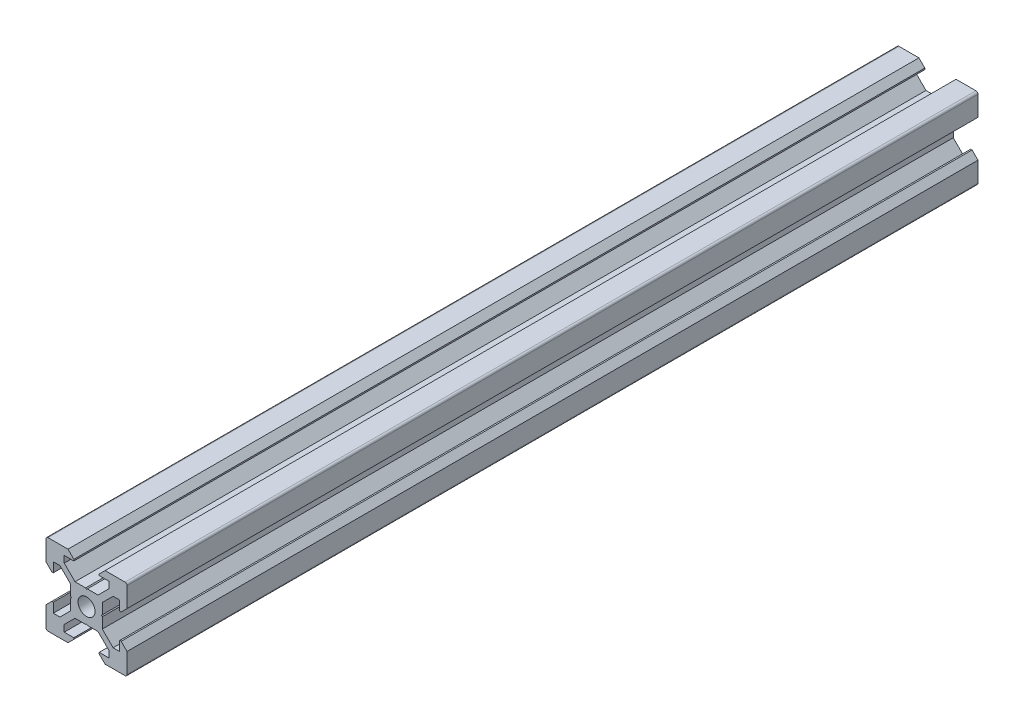
SolidWorks part; units mm, degrees
material "6061-T6 (SS)"
ref_plane "Front Plane" through (0, 0, 0) normal (0, 0, 1) x (1, 0, 0)
ref_plane "Top Plane" through (0, 0, 0) normal (0, 1, 0) x (1, 0, 0)
ref_plane "Right Plane" through (0, 0, 0) normal (1, 0, 0) x (0, 0, -1)
sketch "Sketch1" plane through (0, 0, 0) normal (0, 0, 1) x (1, 0, 0)
  line L1 (9.5, -10) -> (-9.5, -10)
  line L2 (10, -9.5) -> (10, 9.5)
  line L3 (9.5, 10) -> (-9.5, 10)
  line L4 (-10, -9.5) -> (-10, 9.5)
  line L5 (10, -10) -> (-10, 10) construction
  line L6 (10, 10) -> (-10, -10) construction
  circle A0 centre (0, 0) radius 2.1
  arc A1 (-9.5, 10) -> (-10, 9.5) centre (-9.5, 9.5) ccw
  arc A2 (10, 9.5) -> (9.5, 10) centre (9.5, 9.5) ccw
  arc A3 (9.5, -10) -> (10, -9.5) centre (9.5, -9.5) ccw
  arc A4 (-9.5, -10) -> (-10, -9.5) centre (-9.5, -9.5) cw
  point P0 (0, 0)
  line B0 (0, 0) -> (0, 10) construction
  line B1 (0, 3.69) -> (-0.21, 3.9)
  line B2 (-0.21, 3.9) -> (-2.8393, 3.9)
  line B3 (-2.8393, 3.9) -> (-5.5, 6.5607)
  line B4 (-5.5, 6.5607) -> (-5.5, 8.2)
  line B5 (-5.5, 8.2) -> (-3.125, 8.2)
  line B6 (-3.125, 8.2) -> (-3.125, 8.545)
  line B7 (-3.125, 8.545) -> (-4.58, 10)
  line B8 (-4.58, 10) -> (4.58, 10)
  line B9 (0, 0) -> (-5.9132, 5.9132) construction
  line B10 (3.125, 8.545) -> (4.58, 10)
  line B11 (3.125, 8.2) -> (3.125, 8.545)
  line B12 (5.5, 8.2) -> (3.125, 8.2)
  line B13 (5.5, 6.5607) -> (5.5, 8.2)
  line B14 (2.8393, 3.9) -> (5.5, 6.5607)
  line B15 (0.21, 3.9) -> (2.8393, 3.9)
  line B16 (0, 3.69) -> (0.21, 3.9)
  line B17 (0, 0) -> (-10, 0) construction
  line B18 (-3.69, 0) -> (-3.9, -0.21)
  line B19 (-3.9, -0.21) -> (-3.9, -2.8393)
  line B20 (-3.9, -2.8393) -> (-6.5607, -5.5)
  line B21 (-6.5607, -5.5) -> (-8.2, -5.5)
  line B22 (-8.2, -5.5) -> (-8.2, -3.125)
  line B23 (-8.2, -3.125) -> (-8.545, -3.125)
  line B24 (-8.545, -3.125) -> (-10, -4.58)
  line B25 (-10, -4.58) -> (-10, 4.58)
  line B26 (0, 0) -> (-5.9132, -5.9132) construction
  line B27 (-8.545, 3.125) -> (-10, 4.58)
  line B28 (-8.2, 3.125) -> (-8.545, 3.125)
  line B29 (-8.2, 5.5) -> (-8.2, 3.125)
  line B30 (-6.5607, 5.5) -> (-8.2, 5.5)
  line B31 (-3.9, 2.8393) -> (-6.5607, 5.5)
  line B32 (-3.9, 0.21) -> (-3.9, 2.8393)
  line B33 (-3.69, 0) -> (-3.9, 0.21)
  line B34 (0, 0) -> (0, -10) construction
  line B35 (0, -3.69) -> (0.21, -3.9)
  line B36 (0.21, -3.9) -> (2.8393, -3.9)
  line B37 (2.8393, -3.9) -> (5.5, -6.5607)
  line B38 (5.5, -6.5607) -> (5.5, -8.2)
  line B39 (5.5, -8.2) -> (3.125, -8.2)
  line B40 (3.125, -8.2) -> (3.125, -8.545)
  line B41 (3.125, -8.545) -> (4.58, -10)
  line B42 (4.58, -10) -> (-4.58, -10)
  line B43 (0, 0) -> (5.9132, -5.9132) construction
  line B44 (-3.125, -8.545) -> (-4.58, -10)
  line B45 (-3.125, -8.2) -> (-3.125, -8.545)
  line B46 (-5.5, -8.2) -> (-3.125, -8.2)
  line B47 (-5.5, -6.5607) -> (-5.5, -8.2)
  line B48 (-2.8393, -3.9) -> (-5.5, -6.5607)
  line B49 (-0.21, -3.9) -> (-2.8393, -3.9)
  line B50 (0, -3.69) -> (-0.21, -3.9)
  line B51 (0, 0) -> (10, 0) construction
  line B52 (3.69, 0) -> (3.9, 0.21)
  line B53 (3.9, 0.21) -> (3.9, 2.8393)
  line B54 (3.9, 2.8393) -> (6.5607, 5.5)
  line B55 (6.5607, 5.5) -> (8.2, 5.5)
  line B56 (8.2, 5.5) -> (8.2, 3.125)
  line B57 (8.2, 3.125) -> (8.545, 3.125)
  line B58 (8.545, 3.125) -> (10, 4.58)
  line B59 (10, 4.58) -> (10, -4.58)
  line B60 (0, 0) -> (5.9132, 5.9132) construction
  line B61 (8.545, -3.125) -> (10, -4.58)
  line B62 (8.2, -3.125) -> (8.545, -3.125)
  line B63 (8.2, -5.5) -> (8.2, -3.125)
  line B64 (6.5607, -5.5) -> (8.2, -5.5)
  line B65 (3.9, -2.8393) -> (6.5607, -5.5)
  line B66 (3.9, -0.21) -> (3.9, -2.8393)
  line B67 (3.69, 0) -> (3.9, -0.21)
  dimension "D1" = 4.2
  dimension "D3" = 0.5
  dimension "D2" = 20
sketch_block_instance "V Slot 1-4"
sketch_block "V Slot 1" parameters "D1"=10, "D2"=11, "D3"=4.3, "D4"=1.8, "D5"=0.21, "D6"=45, "D7"=9.16, "D8"=1.5, "D9"=6.25
sketch_block_instance "V Slot 1-5"
sketch_block_instance "V Slot 1-6"
sketch_block_instance "V Slot 1-7"
extrude "Boss-Extrude1" add sketch "Sketch1" along normal blind 210 contours B67 B52 B53 B54 B55 B56 B57 B58 L2 A2 L3 B10 B11 B12 B13 B14 B15 B16 B1 B2 B3 B4 B5 B6 B7 A1 L4 B27 B28 B29 B30 B31 B32 B33 B18 B19 B20 B21 B22 B23 B24 A4 L1 B44 B45 B46 B47 B48 B49
